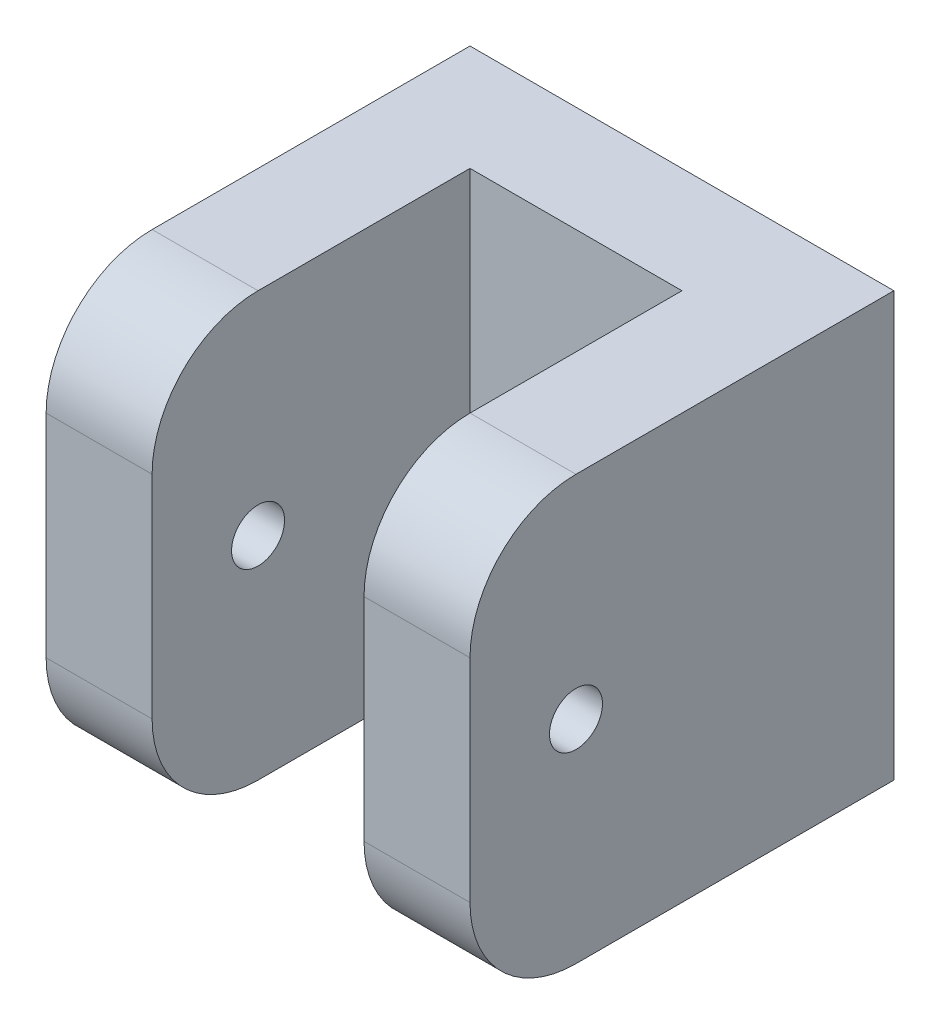
SolidWorks part; units mm, degrees
material "Polyetheretherketone (PEEK)"
ref_plane "Front Plane" through (0, 0, 0) normal (0, 0, 1) x (1, 0, 0)
ref_plane "Top Plane" through (0, 0, 0) normal (0, 1, 0) x (1, 0, 0)
ref_plane "Right Plane" through (0, 0, 0) normal (1, 0, 0) x (0, 0, -1)
sketch "Sketch1" plane through (0, 0, 0) normal (0, 1, 0) x (1, 0, 0)
  line L1 (25.4, -25.4) -> (-25.4, -25.4)
  line L2 (25.4, -25.4) -> (25.4, 25.4)
  line L3 (25.4, 25.4) -> (-25.4, 25.4)
  line L4 (-25.4, -25.4) -> (-25.4, 25.4)
  line L5 (25.4, -25.4) -> (-25.4, 25.4) construction
  line L6 (25.4, 25.4) -> (-25.4, -25.4) construction
  point P0 (0, 0)
  dimension "D1" = 50.8
  dimension "D2" = 50.8
extrude "Boss-Extrude1" add sketch "Sketch1" along normal blind 50.8
sketch "Sketch2" plane through (0, 50.8, 0) normal (0, 1, 0) x (1, 0, 0)
  line L0 (-25.4, -25.4) -> (25.4, -25.4) construction
  line L1 (-12.7, -25.4) -> (12.7, -25.4)
  line L2 (-12.7, -25.4) -> (-12.7, 12.7)
  line L3 (-12.7, 12.7) -> (12.7, 12.7)
  line L4 (12.7, -25.4) -> (12.7, 12.7)
  line L5 (25.4, 25.4) -> (-25.4, 25.4) construction
  dimension "D1" = 12.7
  dimension "D2" = 25.4
  dimension "D3" = 12.7
extrude "Cut-Extrude1" cut sketch "Sketch2" against normal through all
sketch "Sketch3" plane through (0, 0, -12.7) normal (0, 0, 1) x (1, 0, 0)
  line L0 (12.7, 0) -> (-12.7, 0) construction
  line L1 (25.4, 50.8) -> (25.4, 0) construction
  circle A0 centre (0, 25.4) radius 3.175
  dimension "D2" = 25.4
  dimension "D1" = 6.35
  dimension "D3" = 25.4
extrude "Cut-Extrude2" cut sketch "Sketch3" against normal through all
sketch "Sketch4" plane through (25.4, 0, 0) normal (1, 0, 0) x (0, 0, -1)
  line L0 (-25.4, 0) -> (25.4, 0) construction
  line L1 (-25.4, 50.8) -> (-25.4, 0) construction
  circle A0 centre (-12.7, 25.4) radius 3.175
  dimension "D2" = 25.4
  dimension "D3" = 12.7
  dimension "D1" = 6.35
extrude "Cut-Extrude3" cut sketch "Sketch4" against normal through all
fillet "Fillet1" radius 12.7 4 edges at (-19.05, 0, 25.4) (19.05, 0, 25.4) (19.05, 50.8, 25.4) (-19.05, 50.8, 25.4)
equation "\"ScopeLengthUnit\"= 10 * \"ScaleFactor\""
equation "\"EyepieceRadius\"= 0.75 * \"ScaleFactor\""
equation "\"ScopeThickness\"= 0.1 * \"ScaleFactor\""
equation "\"ScopeLensWidth\"= 2 * \"ScaleFactor\""
equation "\"ScopeOutsideRadius\"= 2.1 * \"ScaleFactor\""
equation "\"PegWidth\"=1"
equation "\"SupportOutsideDiam\"= \"ScopeOutsideRadius\" * 2 + .25"
equation "\"RotatingDiskDiam\"=3"
equation "\"LegSeatWidth\"=4 "
equation "\"RotatingDiskHousingDiameter\"= (\"RotatingDiskDiam\" + 2)"
equation "\"LegSeatHeight\"=2"
equation "\"BoltCircleDiam\"= ( \"RotatingDiskDiam\" + \"RotatingDiskHousingDiameter\" ) / 2"
equation "\"D1@Boss-Extrude1\"=\"LegSeatHeight\""
equation "\"D1@Sketch1\"=\"LegSeatWidth\"/2"
equation "\"D2@Sketch1\"=\"LegSeatWidth\"/2"
equation "\"D2@Sketch2\"=\"LegSeatWidth\"/4"
equation "\"D1@Sketch2\"=\"LegSeatWidth\"/8"
equation "\"LegBoltDiam\"=0.25"
equation "\"D1@Sketch3\"=\"LegBoltDiam\""
equation "\"D2@Sketch3\"=\"LegSeatHeight\"/2"
equation "\"D3@Sketch3\"=\"LegSeatWidth\"/4"
equation "\"D1@Sketch4\"=\"LegBoltDiam\""
equation "\"D2@Sketch4\"=\"LegSeatHeight\"/2"
equation "\"D3@Sketch4\"=\"LegSeatWidth\"/8"
equation "\"LegThickness\"=0.25"
equation "\"LegHeight\"=48"
equation "\"PinHeight\"=\"RotDiskLidHeight\" + \"RotDiskHeight\" + \"PinBoltDiam\"*3"
equation "\"PinBoltDiam\"=0.25"
equation "\"RotDiskHeight\"=0.5"
equation "\"RotDiskLidHeight\"= 0.5"
equation "\"DiskSeatPinDiam\"=0.25"
equation "\"ScaleFactor\"= 1"
